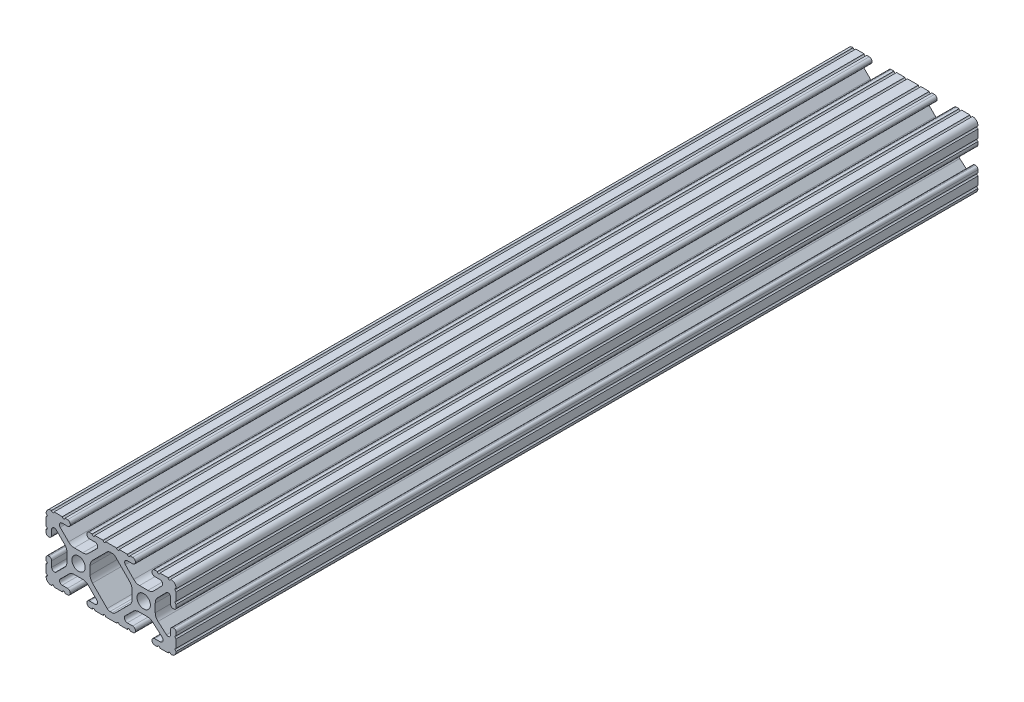
SolidWorks part; units mm, degrees
ref_plane "Front Plane" through (0, 0, 0) normal (0, 0, 1) x (1, 0, 0)
ref_plane "Top Plane" through (0, 0, 0) normal (0, 1, 0) x (1, 0, 0)
ref_plane "Right Plane" through (0, 0, 0) normal (1, 0, 0) x (0, 0, -1)
sketch "Sketch1" plane through (0, 0, 0) normal (0, 0, 1) x (1, 0, 0)
  line L0 (-7.2595, -3.8694) -> (-1.5457, -9.5728)
  line L1 (-8.1915, 1.6223) -> (-8.1915, -1.6223)
  line L2 (-1.504, 9.5765) -> (-7.252, 3.8768)
  line L3 (0.5515, 10.033) -> (-0.3952, 10.033)
  line L4 (7.2829, 3.8459) -> (1.6756, 9.5611)
  line L5 (8.1915, -1.6223) -> (8.1915, 1.6223)
  line L6 (1.5457, -9.5728) -> (7.2595, -3.8694)
  line L7 (-0.4332, -10.033) -> (0.4332, -10.033)
  line L8 (18.0171, 12.7) -> (16.9875, 12.7)
  line L9 (15.9385, 11.651) -> (15.9385, 11.5392)
  line L10 (16.9875, 10.4902) -> (19.1164, 10.4902)
  line L11 (19.8441, 8.7652) -> (16.619, 5.4551)
  line L12 (14.3449, 4.4958) -> (11.0833, 4.4958)
  line L13 (8.817, 5.4472) -> (5.5642, 8.7627)
  line L14 (6.2894, 10.4902) -> (8.4125, 10.4902)
  line L15 (9.4615, 11.5392) -> (9.4615, 11.651)
  line L16 (8.4125, 12.7) -> (7.3829, 12.7)
  line L17 (6.3669, 12.7) -> (3.1496, 12.7)
  line L18 (2.1336, 12.7) -> (-2.1336, 12.7)
  line L19 (-3.1496, 12.7) -> (-6.3669, 12.7)
  line L20 (-7.3829, 12.7) -> (-8.4125, 12.7)
  line L21 (-9.4615, 11.651) -> (-9.4615, 11.5392)
  line L22 (-8.4125, 10.4902) -> (-6.2836, 10.4902)
  line L23 (-5.5326, 8.6661) -> (-8.81, 5.4163)
  line L24 (-11.0455, 4.4958) -> (-14.3545, 4.4958)
  line L25 (-16.59, 5.4163) -> (-19.8674, 8.6661)
  line L26 (-19.1164, 10.4902) -> (-16.9875, 10.4902)
  line L27 (-15.9385, 11.5392) -> (-15.9385, 11.651)
  line L28 (-16.9875, 12.7) -> (-18.0171, 12.7)
  line L29 (-19.0331, 12.7) -> (-22.2504, 12.7)
  line L30 (-25.4, 9.5504) -> (-25.4, 6.3331)
  line L31 (-25.4, 5.3171) -> (-25.4, 4.2375)
  line L32 (-24.401, 3.2385) -> (-24.2392, 3.2385)
  line L33 (-23.1902, 4.2875) -> (-23.1902, 6.3347)
  line L34 (-21.434, 7.0665) -> (-18.148, 3.8082)
  line L35 (-17.2085, 1.5536) -> (-17.2085, -1.6952)
  line L36 (-18.1405, -3.9423) -> (-21.4316, -7.2274)
  line L37 (-23.1902, -6.498) -> (-23.1902, -4.2875)
  line L38 (-24.2392, -3.2385) -> (-24.351, -3.2385)
  line L39 (-25.4, -4.2875) -> (-25.4, -5.3171)
  line L40 (-25.4, -6.3331) -> (-25.4, -9.5504)
  line L41 (-22.2504, -12.7) -> (-19.0331, -12.7)
  line L42 (-18.0171, -12.7) -> (-16.9875, -12.7)
  line L43 (-15.9384, -11.651) -> (-15.9384, -11.5392)
  line L44 (-16.9875, -10.4902) -> (-19.1164, -10.4902)
  line L45 (-19.8341, -8.7551) -> (-16.4966, -5.4237)
  line L46 (-14.2536, -4.4958) -> (-11.1464, -4.4958)
  line L47 (-8.9034, -5.4237) -> (-5.5659, -8.7551)
  line L48 (-6.2836, -10.4902) -> (-8.4125, -10.4902)
  line L49 (-9.4616, -11.5392) -> (-9.4616, -11.651)
  line L50 (-8.4125, -12.7) -> (-7.3829, -12.7)
  line L51 (-6.3669, -12.7) -> (-3.1496, -12.7)
  line L52 (-2.1336, -12.7) -> (2.1336, -12.7)
  line L53 (3.1496, -12.7) -> (6.3669, -12.7)
  line L54 (7.3829, -12.7) -> (8.4125, -12.7)
  line L55 (9.4616, -11.651) -> (9.4616, -11.5392)
  line L56 (8.4125, -10.4902) -> (6.2894, -10.4902)
  line L57 (5.4807, -8.5353) -> (8.5979, -5.4237)
  line L58 (10.8409, -4.4958) -> (14.1026, -4.4958)
  line L59 (16.1879, -5.2766) -> (19.8682, -8.4822)
  line L60 (19.1164, -10.4902) -> (16.9875, -10.4902)
  line L61 (15.9384, -11.5392) -> (15.9384, -11.651)
  line L62 (16.9875, -12.7) -> (18.0171, -12.7)
  line L63 (19.0331, -12.7) -> (22.2504, -12.7)
  line L64 (25.4, -9.5504) -> (25.4, -6.3331)
  line L65 (25.4, -5.3171) -> (25.4, -4.2375)
  line L66 (24.401, -3.2385) -> (24.1892, -3.2385)
  line L67 (23.1902, -4.2375) -> (23.1902, -6.1559)
  line L68 (21.584, -6.8869) -> (18.2982, -4.025)
  line L69 (17.2085, -1.6308) -> (17.2085, 1.6308)
  line L70 (18.1094, 3.8465) -> (21.5263, 7.3534)
  line L71 (23.1902, 6.6769) -> (23.1902, 4.2375)
  line L72 (24.1892, 3.2385) -> (24.401, 3.2385)
  line L73 (25.4, 4.2375) -> (25.4, 5.3171)
  line L74 (25.4, 6.3332) -> (25.4, 9.5504)
  line L75 (22.2504, 12.7) -> (19.0331, 12.7)
  circle A0 centre (-12.7, 0) radius 2.6035
  circle A1 centre (12.7, 0) radius 2.6035
  arc A2 (-1.5457, -9.5728) -> (-0.4332, -10.033) centre (-0.4332, -8.4582) ccw
  arc A3 (-8.1915, -1.6223) -> (-7.2595, -3.8694) centre (-5.0165, -1.6223) ccw
  arc A4 (-7.252, 3.8768) -> (-8.1915, 1.6223) centre (-5.0165, 1.6223) ccw
  arc A5 (-0.3952, 10.033) -> (-1.504, 9.5765) centre (-0.3952, 8.4582) ccw
  arc A6 (1.6756, 9.5611) -> (0.5515, 10.033) centre (0.5515, 8.4582) ccw
  arc A7 (8.1915, 1.6223) -> (7.2829, 3.8459) centre (5.0165, 1.6223) ccw
  arc A8 (7.2595, -3.8694) -> (8.1915, -1.6223) centre (5.0165, -1.6223) ccw
  arc A9 (0.4332, -10.033) -> (1.5457, -9.5728) centre (0.4332, -8.4582) ccw
  arc A10 (18.0171, 12.7) -> (19.0331, 12.7) centre (18.5251, 12.7) ccw
  arc A11 (16.9875, 12.7) -> (15.9385, 11.651) centre (16.9875, 11.651) ccw
  arc A12 (15.9385, 11.5392) -> (16.9875, 10.4902) centre (16.9875, 11.5392) ccw
  arc A13 (19.8441, 8.7652) -> (19.1164, 10.4902) centre (19.1164, 9.4742) ccw
  arc A14 (14.3449, 4.4958) -> (16.619, 5.4551) centre (14.3449, 7.6708) ccw
  arc A15 (8.817, 5.4472) -> (11.0833, 4.4958) centre (11.0833, 7.6708) ccw
  arc A16 (6.2894, 10.4902) -> (5.5642, 8.7627) centre (6.2894, 9.4742) ccw
  arc A17 (8.4125, 10.4902) -> (9.4615, 11.5392) centre (8.4125, 11.5392) ccw
  arc A18 (9.4615, 11.651) -> (8.4125, 12.7) centre (8.4125, 11.651) ccw
  arc A19 (6.3669, 12.7) -> (7.3829, 12.7) centre (6.8749, 12.7) ccw
  arc A20 (2.1336, 12.7) -> (3.1496, 12.7) centre (2.6416, 12.7) ccw
  arc A21 (-3.1496, 12.7) -> (-2.1336, 12.7) centre (-2.6416, 12.7) ccw
  arc A22 (-7.3829, 12.7) -> (-6.3669, 12.7) centre (-6.8749, 12.7) ccw
  arc A23 (-8.4125, 12.7) -> (-9.4615, 11.651) centre (-8.4125, 11.651) ccw
  arc A24 (-9.4615, 11.5392) -> (-8.4125, 10.4902) centre (-8.4125, 11.5392) ccw
  arc A25 (-5.5326, 8.6661) -> (-6.2836, 10.4902) centre (-6.2836, 9.4235) ccw
  arc A26 (-11.0455, 4.4958) -> (-8.81, 5.4163) centre (-11.0455, 7.6708) ccw
  arc A27 (-16.59, 5.4163) -> (-14.3545, 4.4958) centre (-14.3545, 7.6708) ccw
  arc A28 (-19.1164, 10.4902) -> (-19.8674, 8.6661) centre (-19.1164, 9.4235) ccw
  arc A29 (-16.9875, 10.4902) -> (-15.9385, 11.5392) centre (-16.9875, 11.5392) ccw
  arc A30 (-15.9385, 11.651) -> (-16.9875, 12.7) centre (-16.9875, 11.651) ccw
  arc A31 (-19.0331, 12.7) -> (-18.0171, 12.7) centre (-18.5251, 12.7) ccw
  arc A32 (-23.2664, 12.6998) -> (-22.2504, 12.7) centre (-22.7584, 12.7) ccw
  arc A33 (-23.2664, 12.6998) -> (-25.3998, 10.5664) centre (-23.2918, 10.5918) ccw
  arc A34 (-25.4, 9.5504) -> (-25.3998, 10.5664) centre (-25.4, 10.0584) ccw
  arc A35 (-25.4, 5.3171) -> (-25.4, 6.3331) centre (-25.4, 5.8251) ccw
  arc A36 (-25.4, 4.2375) -> (-24.401, 3.2385) centre (-24.401, 4.2375) ccw
  arc A37 (-24.2392, 3.2385) -> (-23.1902, 4.2875) centre (-24.2392, 4.2875) ccw
  arc A38 (-21.434, 7.0665) -> (-23.1902, 6.3347) centre (-22.1596, 6.3347) ccw
  arc A39 (-17.2085, 1.5536) -> (-18.148, 3.8082) centre (-20.3835, 1.5536) ccw
  arc A40 (-18.1405, -3.9423) -> (-17.2085, -1.6952) centre (-20.3835, -1.6952) ccw
  arc A41 (-23.1902, -6.498) -> (-21.4316, -7.2274) centre (-22.1596, -6.498) ccw
  arc A42 (-23.1902, -4.2875) -> (-24.2392, -3.2385) centre (-24.2392, -4.2875) ccw
  arc A43 (-24.351, -3.2385) -> (-25.4, -4.2875) centre (-24.351, -4.2875) ccw
  arc A44 (-25.4, -6.3331) -> (-25.4, -5.3171) centre (-25.4, -5.8251) ccw
  arc A45 (-25.3998, -10.5664) -> (-25.4, -9.5504) centre (-25.4, -10.0584) ccw
  arc A46 (-25.3998, -10.5664) -> (-23.2664, -12.6998) centre (-23.2918, -10.5918) ccw
  arc A47 (-22.2504, -12.7) -> (-23.2664, -12.6998) centre (-22.7584, -12.7) ccw
  arc A48 (-18.0171, -12.7) -> (-19.0331, -12.7) centre (-18.5251, -12.7) ccw
  arc A49 (-16.9875, -12.7) -> (-15.9384, -11.651) centre (-16.9875, -11.651) ccw
  arc A50 (-15.9384, -11.5392) -> (-16.9875, -10.4902) centre (-16.9875, -11.5392) ccw
  arc A51 (-19.8341, -8.7551) -> (-19.1164, -10.4902) centre (-19.1164, -9.4742) ccw
  arc A52 (-14.2536, -4.4958) -> (-16.4966, -5.4237) centre (-14.2536, -7.6708) ccw
  arc A53 (-8.9034, -5.4237) -> (-11.1464, -4.4958) centre (-11.1464, -7.6708) ccw
  arc A54 (-6.2836, -10.4902) -> (-5.5659, -8.7551) centre (-6.2836, -9.4742) ccw
  arc A55 (-8.4125, -10.4902) -> (-9.4616, -11.5392) centre (-8.4125, -11.5392) ccw
  arc A56 (-9.4616, -11.651) -> (-8.4125, -12.7) centre (-8.4125, -11.651) ccw
  arc A57 (-6.3669, -12.7) -> (-7.3829, -12.7) centre (-6.8749, -12.7) ccw
  arc A58 (-2.1336, -12.7) -> (-3.1496, -12.7) centre (-2.6416, -12.7) ccw
  arc A59 (3.1496, -12.7) -> (2.1336, -12.7) centre (2.6416, -12.7) ccw
  arc A60 (7.3829, -12.7) -> (6.3669, -12.7) centre (6.8749, -12.7) ccw
  arc A61 (8.4125, -12.7) -> (9.4616, -11.651) centre (8.4125, -11.651) ccw
  arc A62 (9.4616, -11.5392) -> (8.4125, -10.4902) centre (8.4125, -11.5392) ccw
  arc A63 (5.4807, -8.5353) -> (6.2894, -10.4902) centre (6.2894, -9.3455) ccw
  arc A64 (10.8409, -4.4958) -> (8.5979, -5.4237) centre (10.8409, -7.6708) ccw
  arc A65 (16.1879, -5.2766) -> (14.1026, -4.4958) centre (14.1026, -7.6708) ccw
  arc A66 (19.1164, -10.4902) -> (19.8682, -8.4822) centre (19.1164, -9.3455) ccw
  arc A67 (16.9875, -10.4902) -> (15.9384, -11.5392) centre (16.9875, -11.5392) ccw
  arc A68 (15.9384, -11.651) -> (16.9875, -12.7) centre (16.9875, -11.651) ccw
  arc A69 (19.0331, -12.7) -> (18.0171, -12.7) centre (18.5251, -12.7) ccw
  arc A70 (23.2664, -12.6998) -> (22.2504, -12.7) centre (22.7584, -12.7) ccw
  arc A71 (23.2664, -12.6998) -> (25.3998, -10.5664) centre (23.2918, -10.5918) ccw
  arc A72 (25.4, -9.5504) -> (25.3998, -10.5664) centre (25.4, -10.0584) ccw
  arc A73 (25.4, -5.3171) -> (25.4, -6.3331) centre (25.4, -5.8251) ccw
  arc A74 (25.4, -4.2375) -> (24.401, -3.2385) centre (24.401, -4.2375) ccw
  arc A75 (24.1892, -3.2385) -> (23.1902, -4.2375) centre (24.1892, -4.2375) ccw
  arc A76 (21.584, -6.8869) -> (23.1902, -6.1559) centre (22.2207, -6.1559) ccw
  arc A77 (17.2085, -1.6308) -> (18.2982, -4.025) centre (20.3835, -1.6308) ccw
  arc A78 (18.1094, 3.8465) -> (17.2085, 1.6308) centre (20.3835, 1.6308) ccw
  arc A79 (23.1902, 6.6769) -> (21.5263, 7.3534) centre (22.2207, 6.6769) ccw
  arc A80 (23.1902, 4.2375) -> (24.1892, 3.2385) centre (24.1892, 4.2375) ccw
  arc A81 (24.401, 3.2385) -> (25.4, 4.2375) centre (24.401, 4.2375) ccw
  arc A82 (25.4, 6.3332) -> (25.4, 5.3171) centre (25.4, 5.8251) ccw
  arc A83 (25.3998, 10.5664) -> (25.4, 9.5504) centre (25.4, 10.0584) ccw
  arc A84 (25.3998, 10.5664) -> (23.2664, 12.6998) centre (23.2918, 10.5918) ccw
  arc A85 (22.2504, 12.7) -> (23.2664, 12.6998) centre (22.7584, 12.7) ccw
  point P248 (0, 10.033)
extrude "Boss-Extrude1" add sketch "Sketch1" along normal mid plane 312.7
